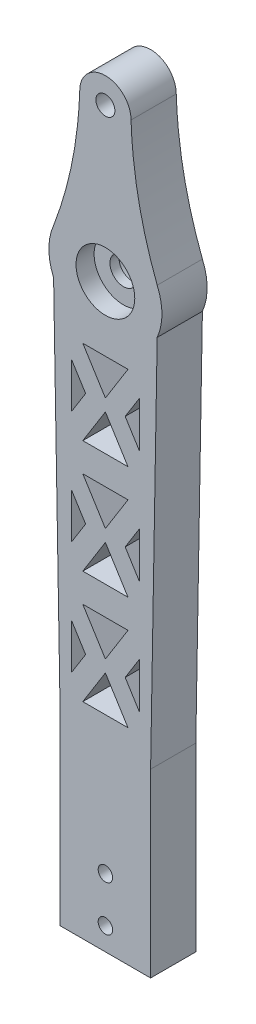
SolidWorks part; units mm, degrees
ref_plane "Front Plane" through (0, 0, 0) normal (0, 0, 1) x (1, 0, 0)
ref_plane "Top Plane" through (0, 0, 0) normal (0, 1, 0) x (1, 0, 0)
ref_plane "Right Plane" through (0, 0, 0) normal (1, 0, 0) x (0, 0, -1)
sketch "Sketch1" plane through (0, 0, 0) normal (0, 0, 1) x (1, 0, 0)
  line L0 (-11.4564, 83.4393) -> (-10, 0)
  line L5 (10, 0) -> (11.4564, 83.4393)
  line L6 (-17.342, 0) -> (22.2939, 0) construction
  line L7 (-11.4564, 93.4393) -> (11.4564, 93.4393)
  line L10 (0, 88.4393) -> (0, 127.7582) construction
  line L11 (-10, 0) -> (10, 0)
  line L13 (-10, 0) -> (-10, -40)
  line L16 (0, 55.4391) -> (5, 55.4391)
  line L17 (0, 55.4391) -> (-5, 55.4391)
  line L18 (-5, 55.4391) -> (0, 63.4391)
  line L19 (0, 63.4391) -> (5, 55.4391)
  line L20 (7.5, 69.7692) -> (4.375, 64.7692)
  line L21 (4.375, 64.7692) -> (7.5, 59.7692)
  line L22 (7.5, 59.7692) -> (7.5, 69.7692)
  line L23 (-4.375, 64.7692) -> (-7.5, 59.7692)
  line L24 (-7.5, 69.7692) -> (-4.375, 64.7692)
  line L25 (-7.5, 59.7692) -> (-7.5, 69.7692)
  line L26 (0, 64.7692) -> (14.1707, 64.7692) construction
  line L27 (-5, 74.0994) -> (0, 66.0994)
  line L28 (0, 74.0994) -> (-5, 74.0994)
  line L29 (0, 74.0994) -> (5, 74.0994)
  line L30 (0, 66.0994) -> (5, 74.0994)
  line L31 (-4.375, 39.7692) -> (-7.5, 34.7692)
  line L32 (-7.5, 34.7692) -> (-7.5, 44.7692)
  line L33 (-7.5, 44.7692) -> (-4.375, 39.7692)
  line L34 (-5, 49.0994) -> (0, 41.0994)
  line L35 (0, 41.0994) -> (5, 49.0994)
  line L36 (0, 49.0994) -> (5, 49.0994)
  line L37 (0, 49.0994) -> (-5, 49.0994)
  line L38 (7.5, 34.7692) -> (7.5, 44.7692)
  line L39 (7.5, 44.7692) -> (4.375, 39.7692)
  line L40 (4.375, 39.7692) -> (7.5, 34.7692)
  line L41 (0, 38.4391) -> (5, 30.4391)
  line L42 (0, 30.4391) -> (5, 30.4391)
  line L43 (0, 30.4391) -> (-5, 30.4391)
  line L44 (-5, 30.4391) -> (0, 38.4391)
  line L45 (-4.375, 14.7692) -> (-7.5, 9.7692)
  line L46 (-7.5, 9.7692) -> (-7.5, 19.7692)
  line L47 (-7.5, 19.7692) -> (-4.375, 14.7692)
  line L48 (-5, 24.0994) -> (0, 16.0994)
  line L49 (0, 16.0994) -> (5, 24.0994)
  line L50 (0, 24.0994) -> (5, 24.0994)
  line L51 (0, 24.0994) -> (-5, 24.0994)
  line L52 (7.5, 9.7692) -> (7.5, 19.7692)
  line L53 (7.5, 19.7692) -> (4.375, 14.7692)
  line L54 (4.375, 14.7692) -> (7.5, 9.7692)
  line L55 (0, 13.4391) -> (5, 5.4391)
  line L56 (0, 5.4391) -> (5, 5.4391)
  line L57 (0, 5.4391) -> (-5, 5.4391)
  line L58 (-5, 5.4391) -> (0, 13.4391)
  line L59 (-10, -40) -> (10, -40)
  line L60 (10, -40) -> (10, 0)
  circle A1 centre (0, 88.4393) radius 12.5
  arc A3 (5.672, 122.1918) -> (-5.672, 122.1918) centre (0, 122.1918) ccw
  spline S0 degree 2 poles (11.4564, 93.4393) (6.1564, 107.3258) (5.672, 122.1918) knots 0 0 0 1 1 1
  spline S1 degree 2 poles (-11.4564, 93.4393) (-6.1564, 107.3258) (-5.672, 122.1918) knots 0 0 0 1 1 1
  point P16 (0, 88.4393)
  dimension "D11" = 14.9925
  dimension "D10" = 29.4653
  dimension "D9" = 25
  dimension "D15" = 20
  dimension "D16" = 40
  dimension "D14" = 5.672
  dimension "D29" = 5
  dimension "D2" = 91
  dimension "D3" = 0
  dimension "D4" = 0
  dimension "D5" = 5
  dimension "D6" = 5
  dimension "D7" = 0
  dimension "D8" = 5
  dimension "D12" = 13.76
  dimension "D13" = 11.3439
  dimension "D19" = 5
  dimension "D20" = 5
  dimension "D21" = 8
  dimension "D30" = 5
  dimension "D31" = 5
  dimension "D32" = 2.5
  dimension "D33" = 5
  dimension "D34" = 3
extrude "Boss-Extrude1" add sketch "Sketch1" along normal blind 10
sketch "Sketch2" plane through (0, 0, 10) normal (0, 0, 1) x (1, 0, 0)
  circle A0 centre (0, 122.1918) radius 2.1
  circle A3 centre (0, 88.4393) radius 6.5
  dimension "D1" = 4.2
  dimension "D2" = 13
extrude "Cut-Extrude1" cut sketch "Sketch2" against normal blind 4 contours A0 | A3
sketch "Sketch3" plane through (0, 0, 0) normal (0, 0, -1) x (-1, 0, 0)
  circle A0 centre (0, 88.4393) radius 6.5
  dimension "D1" = 13
extrude "Cut-Extrude2" cut sketch "Sketch3" against normal blind 4
sketch "Sketch4" plane through (0, 0, 4) normal (0, 0, -1) x (-1, 0, 0)
  circle A0 centre (0, 88.4393) radius 3
  dimension "D1" = 6
extrude "Cut-Extrude3" cut sketch "Sketch4" against normal through all
sketch "Sketch7" plane through (0, 0, 10) normal (0, 0, 1) x (1, 0, 0)
  line L0 (-10, 0) -> (-10, -40) construction
  line L1 (10, -40) -> (10, 0) construction
  line L2 (-10, -40) -> (10, -40) construction
  circle A0 centre (0, -25) radius 1.6
  circle A1 centre (0, -35) radius 1.6
  dimension "D1" = 3.2
  dimension "D2" = 3.2
  dimension "D3" = 10
  dimension "D4" = 10
  dimension "D5" = 10
  dimension "D6" = 5
extrude "Cut-Extrude6" cut sketch "Sketch7" against normal through all
sketch "Sketch8" plane through (0, 0, 10) normal (0, 0, 1) x (1, 0, 0)
  circle A0 centre (0, 122.1918) radius 2.1
extrude "Cut-Extrude7" cut sketch "Sketch8" against normal through all
